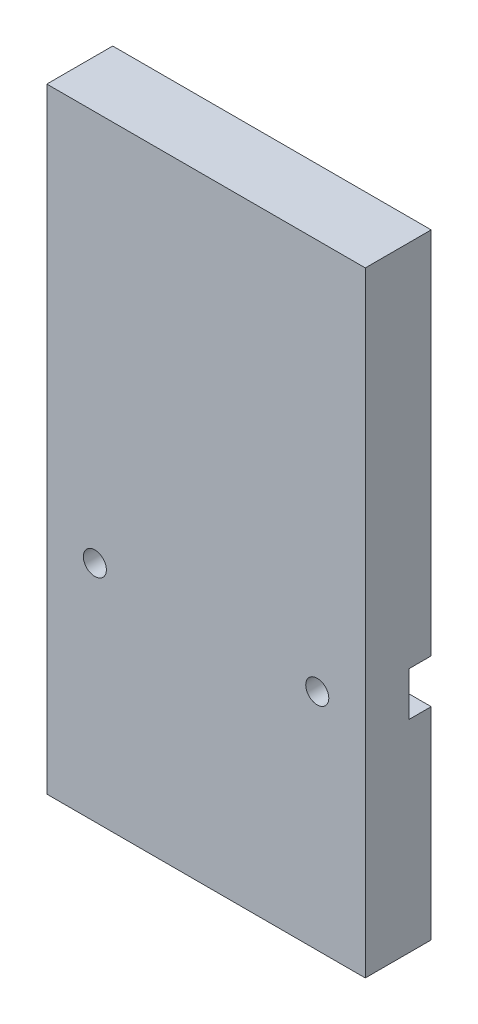
SolidWorks part; units mm, degrees
ref_plane "Front Plane" through (0, 0, 0) normal (0, 0, 1) x (1, 0, 0)
ref_plane "Top Plane" through (0, 0, 0) normal (0, 1, 0) x (1, 0, 0)
ref_plane "Right Plane" through (0, 0, 0) normal (1, 0, 0) x (0, 0, -1)
sketch "Sketch1" plane through (0, 0, 0) normal (0, 1, 0) x (1, 0, 0)
  line L1 (0, 0) -> (184.15, 0)
  line L2 (0, 0) -> (0, 38.1)
  line L3 (0, 38.1) -> (184.15, 38.1)
  line L4 (184.15, 0) -> (184.15, 38.1)
  dimension "D1" = 184.15
  dimension "D2" = 38.1
extrude "Boss-Extrude1" add sketch "Sketch1" along normal blind 355.6
sketch "Sketch2" plane through (0, 0, -38.1) normal (0, 0, 1) x (1, 0, 0)
  line L0 (0, 355.6) -> (0, 0) construction
  line L1 (0, 116.84) -> (184.15, 116.84)
  line L2 (0, 116.84) -> (0, 142.24)
  line L3 (0, 142.24) -> (184.15, 142.24)
  line L4 (184.15, 116.84) -> (184.15, 142.24)
  line L5 (184.15, 355.6) -> (184.15, 0) construction
  line L7 (0, 0) -> (184.15, 0) construction
  dimension "D1" = 25.4
  dimension "D2" = 142.24
extrude "Cut-Extrude1" cut sketch "Sketch2" along normal blind 12.7
sketch "Sketch3" plane through (0, 0, -25.4) normal (0, 0, -1) x (-1, 0, 0)
  line L0 (-184.15, 116.84) -> (-184.15, 142.24) construction
  line L1 (0, 142.24) -> (0, 116.84) construction
  line L2 (-184.15, 129.54) -> (0, 129.54) construction
  circle A0 centre (-156.3741, 129.54) radius 6.6675
  circle A1 centre (-27.7759, 129.54) radius 6.6675
  dimension "D1" = 13.335
  dimension "D2" = 13.335
  dimension "D3" = 27.7759
  dimension "D4" = 27.7759
extrude "Cut-Extrude2" cut sketch "Sketch3" against normal through all both and the other way through all
sketch "Sketch4" plane through (0, 0, 0) normal (0, -1, 0) x (1, 0, 0)
  line L0 (0, 0) -> (184.15, 0)
  line L1 (0, 0) -> (0, -38.1)
  line L2 (0, -38.1) -> (184.15, -38.1)
  line L3 (184.15, 0) -> (184.15, -38.1)
  line L4 (12.7, -19.05) -> (0, -19.05) construction
  line L5 (12.7, -19.05) -> (35.3786, -19.05) construction
  line L6 (35.3786, -19.05) -> (58.0571, -19.05) construction
  line L7 (58.0571, -19.05) -> (80.7357, -19.05) construction
  line L8 (80.7357, -19.05) -> (103.4143, -19.05) construction
  line L9 (103.4143, -19.05) -> (126.0929, -19.05) construction
  line L10 (126.0929, -19.05) -> (148.7714, -19.05) construction
  line L11 (148.7714, -19.05) -> (171.45, -19.05) construction
  line L12 (0, 0) -> (184.15, 0) construction
  line L13 (0, -38.1) -> (0, 0) construction
  circle A0 centre (12.7, -19.05) radius 1.3891 construction
  circle A1 centre (35.3786, -19.05) radius 1.3891 construction
  circle A2 centre (148.7714, -19.05) radius 1.3891 construction
  circle A3 centre (171.45, -19.05) radius 1.3891 construction
  circle A4 centre (58.0571, -19.05) radius 1.3891 construction
  circle A5 centre (126.0929, -19.05) radius 1.3891 construction
  circle A6 centre (80.7357, -19.05) radius 1.3891 construction
  circle A7 centre (103.4143, -19.05) radius 1.3891 construction
  dimension "D3" = 2.7781
  dimension "D1" = 184.15
  dimension "D2" = 38.1
  dimension "D4" = 12.7
  dimension "D5" = 12.7
hole_wizard "#10 (0.1935) Diameter Hole1" positions "3DSketch1" profile "Sketch5" hole size "#10" standard "ANSI Inch"
sketch3d "3DSketch1"
  point P0 (12.7, 0, -19.05)
  point P3 (35.3786, 0, -19.05)
  point P6 (58.0571, 0, -19.05)
  point P9 (80.7357, 0, -19.05)
  point P12 (103.4143, 0, -19.05)
  point P15 (126.0929, 0, -19.05)
  point P18 (148.7714, 0, -19.05)
  point P21 (171.45, 0, -19.05)
sketch "Sketch5" plane through (12.7, 0, -19.05) normal (1, 0, 0) x (0, 0, -1)
  line L0 (0, 0) -> (0, 77.6766)
  line L1 (0, 77.6766) -> (2.4574, 76.2)
  line L2 (2.4574, 76.2) -> (2.4574, 0)
  line L5 (2.4574, 0) -> (0, 0)
  line L10 (0, 77.6766) -> (-2.4575, 76.2) construction
  line L11 (0, -6.35) -> (0, 107.95) construction
  dimension "Hole Dia." = 4.9149
  dimension "Hole Depth" = 76.2
  dimension "Drill Angle" = 118
